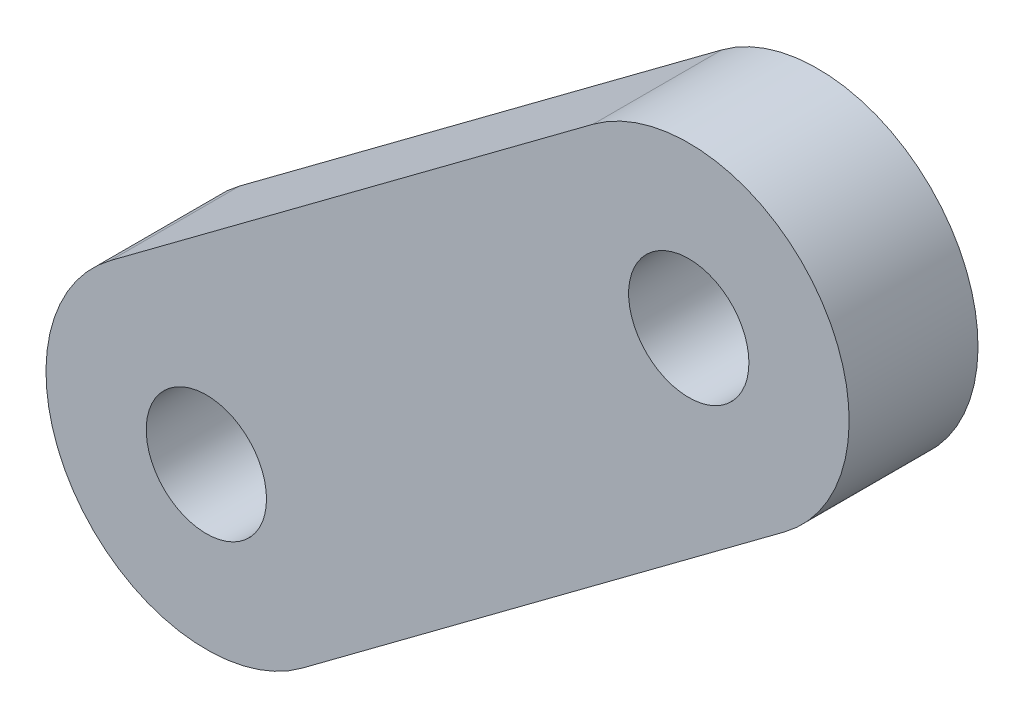
SolidWorks part; units mm, degrees
ref_plane "Front Plane" through (0, 0, 0) normal (0, 0, 1) x (1, 0, 0)
ref_plane "Top Plane" through (0, 0, 0) normal (0, 1, 0) x (1, 0, 0)
ref_plane "Right Plane" through (0, 0, 0) normal (1, 0, 0) x (0, 0, -1)
sketch "Sketch1" plane through (0, 0, 0) normal (0, 0, 1) x (1, 0, 0)
  line L0 (3.9636, 7.0813) -> (-7.2658, -1.2794)
  line L1 (-2.8067, -7.2684) -> (8.4226, 1.0923)
  arc A0 (-7.2658, -1.2794) -> (-2.8067, -7.2684) centre (-5.0363, -4.2739) ccw
  arc A1 (8.4226, 1.0923) -> (3.9636, 7.0813) centre (6.1931, 4.0868) ccw
  circle A2 centre (6.1931, 4.0868) radius 1.4
  circle A3 centre (-5.0363, -4.2739) radius 1.4
  dimension "D1" = 2.8
  dimension "D2" = 2.8
extrude "Boss-Extrude1" add sketch "Sketch1" along normal blind 3
